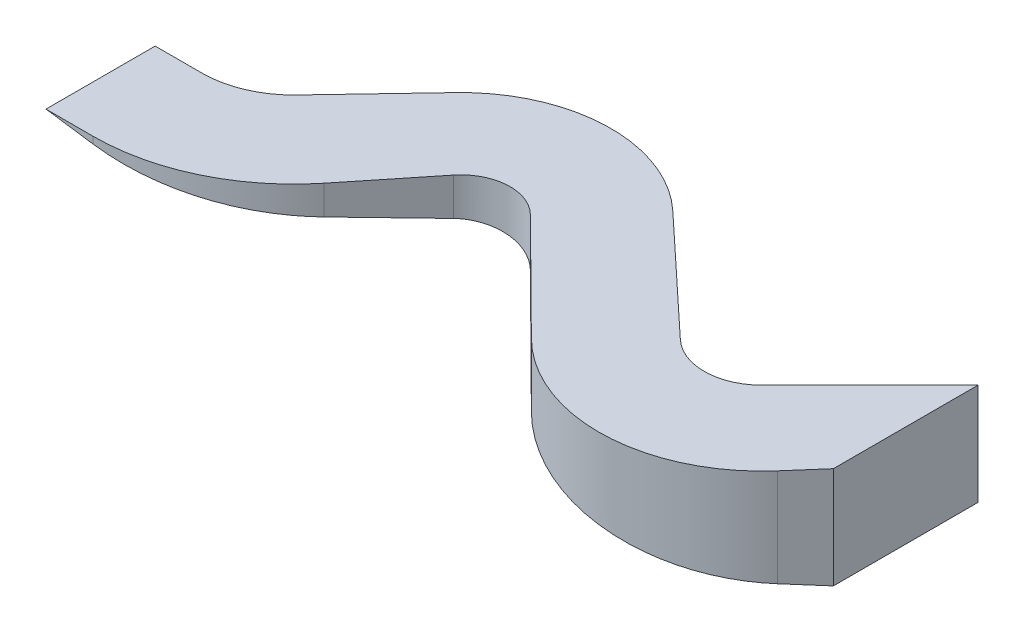
SolidWorks part; units mm, degrees
ref_plane "Front Plane" through (0, 0, 0) normal (0, 0, 1) x (1, 0, 0)
ref_plane "Top Plane" through (0, 0, 0) normal (0, 1, 0) x (1, 0, 0)
ref_plane "Right Plane" through (0, 0, 0) normal (1, 0, 0) x (0, 0, -1)
sketch "Sketch1" plane through (0, 0, 0) normal (0, 1, 0) x (1, 0, 0)
  line L0 (0, 0) -> (0, -854.33)
  line L2 (-3888.2168, -1340.5123) -> (-4165.3845, -1340.5123)
  line L3 (0, 0) -> (-638.3819, -638.3819)
  line L4 (0, -854.33) -> (-154.1905, -1030.8473)
  line L5 (-1112.1267, -646.3636) -> (-1793.5514, -9.3767)
  line L6 (-2194.0515, -450.1976) -> (-1557.1625, -1081.337)
  line L7 (-3496.4939, -527.3602) -> (-3040.4634, -46.7506)
  line L8 (-2624.1801, -474.4607) -> (-2964.8591, -898.1397)
  line L9 (-3888.2168, -695.6706) -> (-4165.3845, -695.6706)
  line L11 (-4165.3845, -695.6706) -> (-4165.3845, -1340.5123)
  arc A0 (-1112.1267, -646.3636) -> (-638.3819, -638.3819) centre (-879.3819, -397.3819) ccw
  arc A2 (-2194.0515, -450.1976) -> (-2624.1801, -474.4607) centre (-2398.1806, -656.1863) ccw
  arc A3 (-1793.5514, -9.3767) -> (-3040.4634, -46.7506) centre (-2398.1806, -656.1863) ccw
  arc A4 (-1557.1625, -1081.337) -> (-154.1905, -1030.8473) centre (-879.3819, -397.3819) ccw
  arc A6 (-3888.2168, -695.6706) -> (-3496.4939, -527.3602) centre (-3888.2168, -155.6706) ccw
  arc A7 (-3888.2168, -1340.5123) -> (-2964.8591, -898.1397) centre (-3888.2168, -155.6706) ccw
extrude "Boss-Extrude3" add sketch "Sketch1" along normal blind 600
sketch "Sketch2" plane through (0, 0, 0) normal (0, 0, 1) x (1, 0, 0)
  line L1 (-4165.3845, 600) -> (0, 0)
  line L3 (-4165.3845, 600) -> (-4165.3845, 0)
  line L4 (0, 0) -> (-4165.3845, 0)
extrude "Cut-Extrude1" cut sketch "Sketch2" against normal blind 2000 and the other way blind 2000 contours L1 L4 L3
